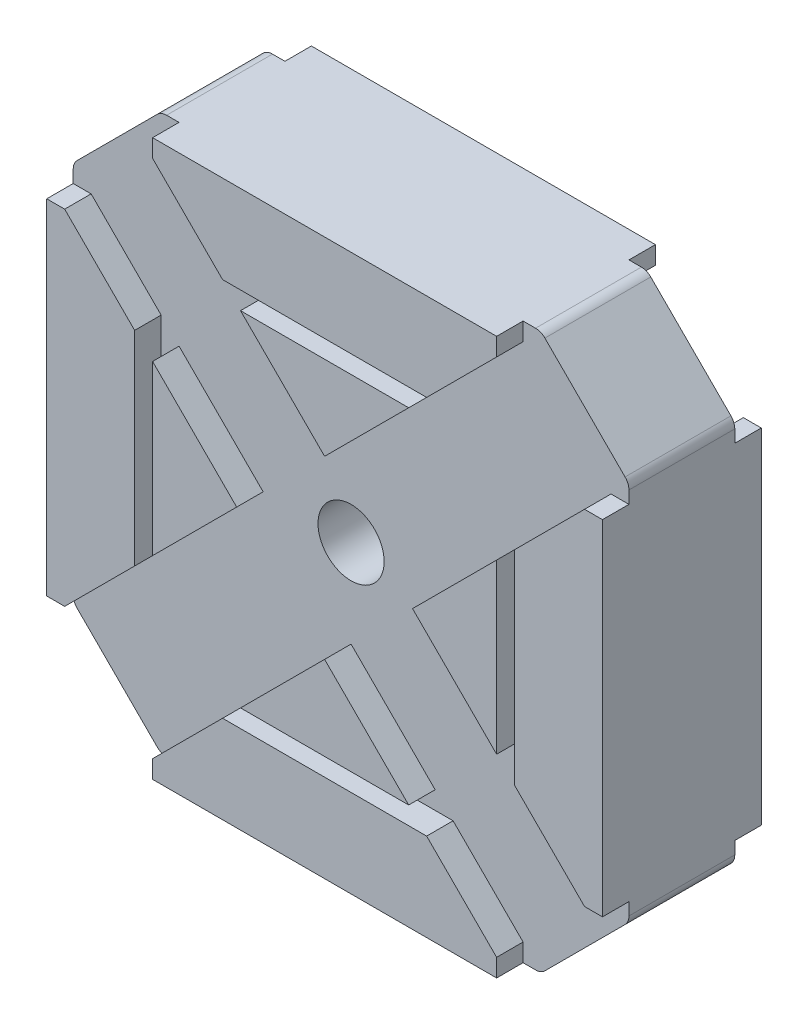
SolidWorks part; units mm, degrees
material "Alumina"
ref_plane "Front" through (0, 0, 0) normal (0, 0, 1) x (1, 0, 0)
ref_plane "Top" through (0, 0, 0) normal (0, 1, 0) x (1, 0, 0)
ref_plane "Right" through (0, 0, 0) normal (1, 0, 0) x (0, 0, -1)
sketch "Sketch1" plane through (0, 0, 0) normal (0, 0, 1) x (1, 0, 0)
  line L0 (-21, 14.3553) -> (-14.3553, 21)
  line L1 (-14.3553, -21) -> (14.3553, -21)
  line L2 (-21, -14.3553) -> (-21, 14.3553)
  line L3 (-14.3553, 21) -> (14.3553, 21)
  line L4 (21, -14.3553) -> (21, 14.3553)
  line L5 (17.6777, 17.6777) -> (-17.6777, -17.6777) construction
  line L6 (-17.6777, 17.6777) -> (17.6777, -17.6777) construction
  line L7 (0, -21) -> (0, 21) construction
  line L8 (-21, 0) -> (21, 0) construction
  line L9 (21, 14.3553) -> (14.3553, 21)
  line L10 (21, -14.3553) -> (14.3553, -21)
  line L11 (-21, -14.3553) -> (-14.3553, -21)
  point P0 (0, 0)
  dimension "D1" = 42
  dimension "D2" = 42
  dimension "D3" = 50
extrude "Boss-Extrude1" add sketch "Sketch1" along normal blind 6
sketch "Sketch2" plane through (0, 21, 0) normal (0, 1, 0) x (1, 0, 0)
  line L0 (0, 0) -> (0, -6) construction
  line L1 (-14.3553, 0) -> (-13, 0)
  line L2 (-14.3553, 0) -> (-14.3553, -2)
  line L3 (-14.3553, -2) -> (-13, -2)
  line L4 (-13, 0) -> (-13, -2)
  line L5 (14.3553, 0) -> (13, 0)
  line L6 (14.3553, 0) -> (14.3553, -2)
  line L7 (14.3553, -2) -> (13, -2)
  line L8 (13, 0) -> (13, -2)
  line L9 (14.3553, 0) -> (-14.3553, 0) construction
  line L10 (14.3553, -6) -> (-14.3553, -6) construction
  line L11 (-13, -2) -> (13, -2) construction
  point P16 (0, -2)
  dimension "D1" = 26
  dimension "D3" = 2
  dimension "D4" = 2
extrude "Cut-Extrude1" cut sketch "Sketch2" against normal through all
sketch "Sketch3" plane through (-21, 0, 0) normal (-1, 0, 0) x (0, 0, 1)
  line L0 (0, 0) -> (6, 0) construction
  line L1 (0, 14.3553) -> (2, 14.3553)
  line L2 (0, 14.3553) -> (0, 13)
  line L3 (0, 13) -> (2, 13)
  line L4 (2, 14.3553) -> (2, 13)
  line L5 (0, -14.3553) -> (2, -14.3553)
  line L6 (0, -14.3553) -> (0, -13)
  line L7 (0, -13) -> (2, -13)
  line L8 (2, -14.3553) -> (2, -13)
  line L9 (0, 14.3553) -> (0, -14.3553) construction
  line L10 (6, 14.3553) -> (6, -14.3553) construction
  line L11 (2, 13) -> (2, -13) construction
  line L12 (2, -13) -> (1.962, -13.1362) construction
  point P16 (2, 0)
  dimension "D1" = 26
  dimension "D3" = 2
  dimension "D4" = 2
extrude "Cut-Extrude2" cut sketch "Sketch3" against normal through all
sketch "Sketch4" plane through (17.6777, 17.6777, 0) normal (0.7071, 0.7071, 0) x (0, 0, -1)
  line L2 (0, 4.6985) -> (-2, 4.6985)
  line L3 (0, 4.6985) -> (0, -4.6985)
  line L4 (0, -4.6985) -> (-2, -4.6985)
  line L5 (-2, 4.6985) -> (-2, -4.6985)
extrude "Cut-Extrude3" cut sketch "Sketch4" against normal through all
sketch "Sketch5" plane through (-17.6777, 17.6777, 0) normal (-0.7071, 0.7071, 0) x (0, 0, 1)
  line L1 (0, 4.6985) -> (2, 4.6985)
  line L2 (0, 4.6985) -> (0, -4.6985)
  line L3 (0, -4.6985) -> (2, -4.6985)
  line L4 (2, 4.6985) -> (2, -4.6985)
extrude "Cut-Extrude4" cut sketch "Sketch5" against normal through all
sketch "Sketch7" plane through (0, 0, 0) normal (0, 0, -1) x (-1, 0, 0)
  circle A0 centre (0, 0) radius 2.5
  dimension "D1" = 5
extrude "Cut-Extrude7" cut sketch "Sketch7" against normal through all
mirror "Mirror2" about plane through (0, 0, 6) normal (0, 0, -1) of "Cut-Extrude7", "Boss-Extrude1", "Cut-Extrude4", "Cut-Extrude3", "Cut-Extrude2", "Cut-Extrude1"
fillet "Fillet1" radius 1 8 edges at (21, -14.3553, 6) (14.3553, -21, 6) (-14.3553, -21, 6) (-21, -14.3553, 6) (-21, 14.3553, 6) (-14.3553, 21, 6) (21, 14.3553, 6) (14.3553, 21, 6)
